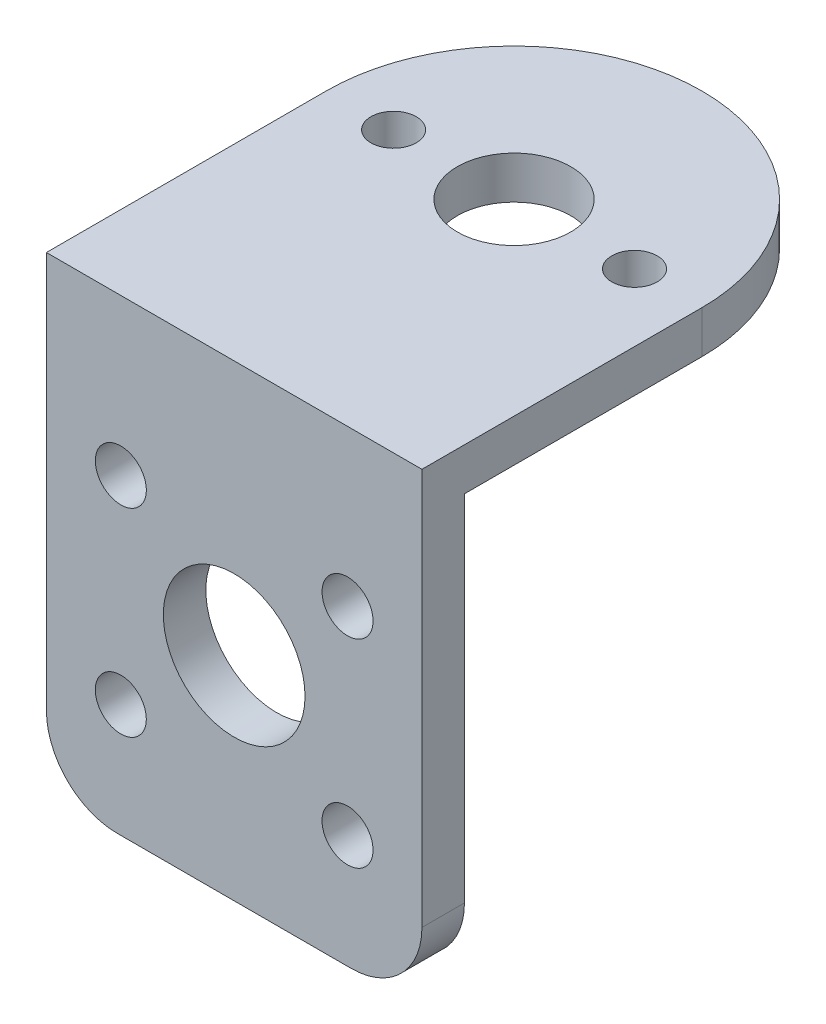
SolidWorks part; units mm, degrees
ref_plane "Front" through (0, 0, 0) normal (0, 0, 1) x (1, 0, 0)
ref_plane "Top" through (0, 0, 0) normal (0, 1, 0) x (1, 0, 0)
ref_plane "Right" through (0, 0, 0) normal (1, 0, 0) x (0, 0, -1)
sketch "草图1" plane through (0, 0, 0) normal (0, 0, 1) x (1, 0, 0)
  line L1 (5, 0) -> (21.5, 0)
  line L2 (0, 5) -> (0, 30)
  line L3 (0, 30) -> (26.5, 30)
  line L4 (26.5, 5) -> (26.5, 30)
  circle A0 centre (13.25, 15) radius 5
  circle A1 centre (5.25, 8) radius 1.8
  circle A2 centre (5.25, 22) radius 1.8
  circle A3 centre (21.25, 8) radius 1.8
  circle A4 centre (21.25, 22) radius 1.8
  arc A5 (5, 0) -> (0, 5) centre (5, 5) cw
  arc A6 (26.5, 5) -> (21.5, 0) centre (21.5, 5) cw
  point P11 (0, 0)
  dimension "D1" = 8
  dimension "D3" = 5
  dimension "D4" = 5
  dimension "D2" = 5.25
extrude "凸台-拉伸1" add sketch "草图1" along normal blind 3
sketch "草图3" plane through (0, 30, 0) normal (0, 1, 0) x (1, 0, 0)
  line L1 (0, -3) -> (26.5, -3)
  line L2 (0, -3) -> (0, 16.75)
  line L4 (26.5, -3) -> (26.5, 16.75)
  arc A0 (26.5, 16.75) -> (0, 16.75) centre (13.25, 16.75) ccw
  circle A1 centre (13.25, 16.75) radius 4
  circle A2 centre (21.75, 16.75) radius 1.6
  circle A3 centre (4.75, 16.75) radius 1.6
  dimension "D1" = 8.5
  dimension "D2" = 8.5
extrude "凸台-拉伸2" add sketch "草图3" along normal blind 3
